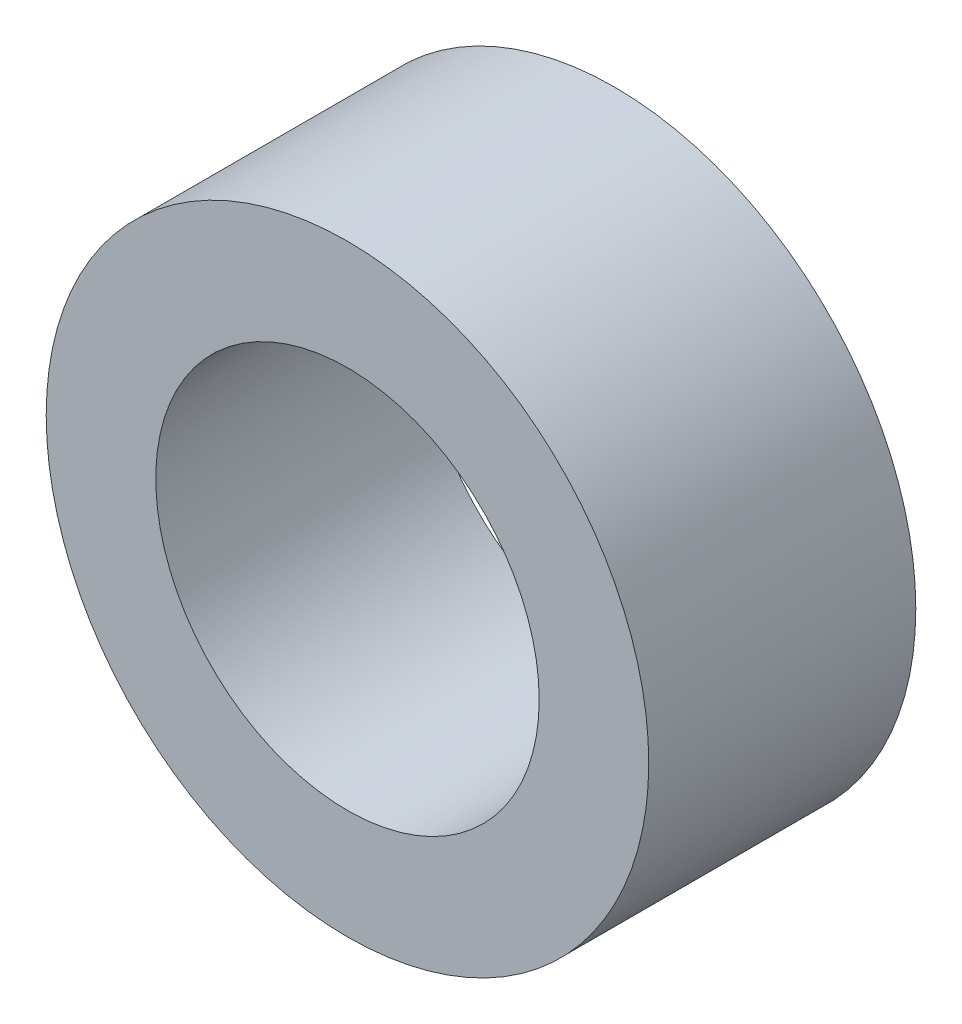
SolidWorks part; units mm, degrees
material "Natural Rubber"
ref_plane "Front Plane" through (0, 0, 0) normal (0, 0, 1) x (1, 0, 0)
ref_plane "Top Plane" through (0, 0, 0) normal (0, 1, 0) x (1, 0, 0)
ref_plane "Right Plane" through (0, 0, 0) normal (1, 0, 0) x (0, 0, -1)
sketch "Sketch1" plane through (0, 0, 0) normal (0, 0, 1) x (1, 0, 0)
  circle A0 centre (0, 0) radius 44
  circle A1 centre (0, 0) radius 28
  dimension "D1" = 88
  dimension "D2" = 56
extrude "Boss-Extrude1" add sketch "Sketch1" along normal blind 39
